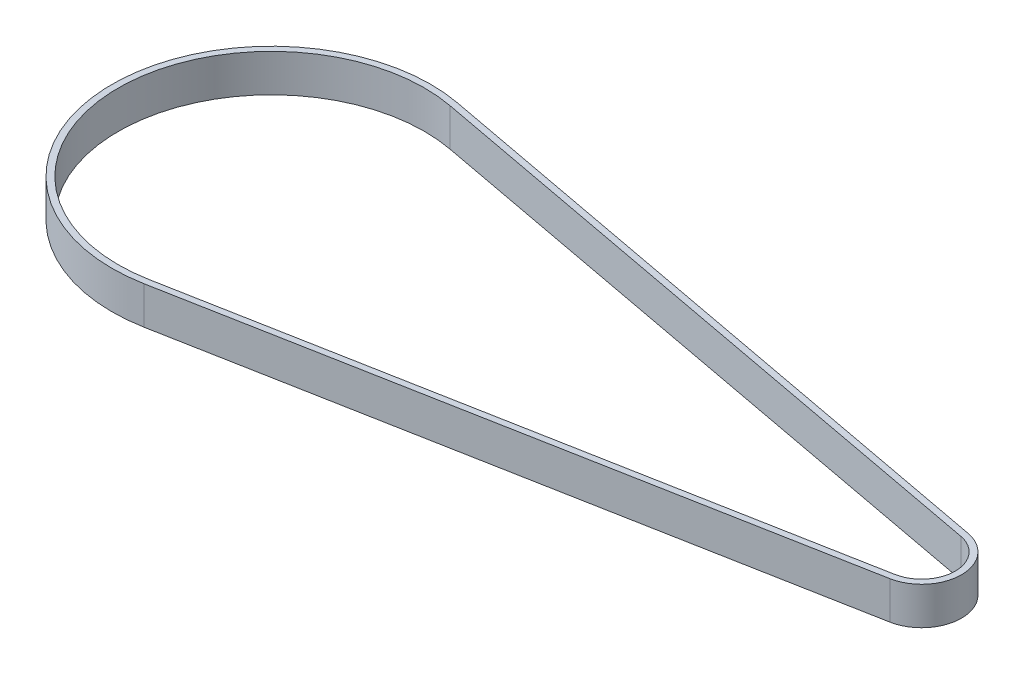
SolidWorks part; units mm, degrees
ref_plane "Alzado" through (0, 0, 0) normal (0, 0, 1) x (1, 0, 0)
ref_plane "Planta" through (0, 0, 0) normal (0, 1, 0) x (1, 0, 0)
ref_plane "Vista lateral" through (0, 0, 0) normal (1, 0, 0) x (0, 0, -1)
sketch "Croquis1" plane through (0, 0, 0) normal (0, 1, 0) x (1, 0, 0)
  line L0 (0, 0) -> (103.6164, 0) construction
  line L1 (4.6698, 24.967) -> (104.7839, 6.2418)
  line L2 (4.6698, -24.967) -> (104.7839, -6.2418)
  line L5 (4.486, 23.9841) -> (104.6, 5.2588)
  line L6 (4.486, -23.9841) -> (104.6, -5.2588)
  arc A0 (4.6698, 24.967) -> (4.6698, -24.967) centre (0, 0) ccw
  arc A1 (104.7839, -6.2418) -> (104.7839, 6.2418) centre (103.6164, 0) ccw
  arc A4 (104.6, -5.2588) -> (104.6, 5.2588) centre (103.6164, 0) ccw
  arc A5 (4.486, 23.9841) -> (4.486, -23.9841) centre (0, 0) ccw
  dimension "D1" = 103.6164
  dimension "D2" = 50.8
  dimension "D3" = 12.7
  dimension "D5" = 1
extrude "Saliente-Extruir1" add sketch "Croquis1" along normal blind 6
